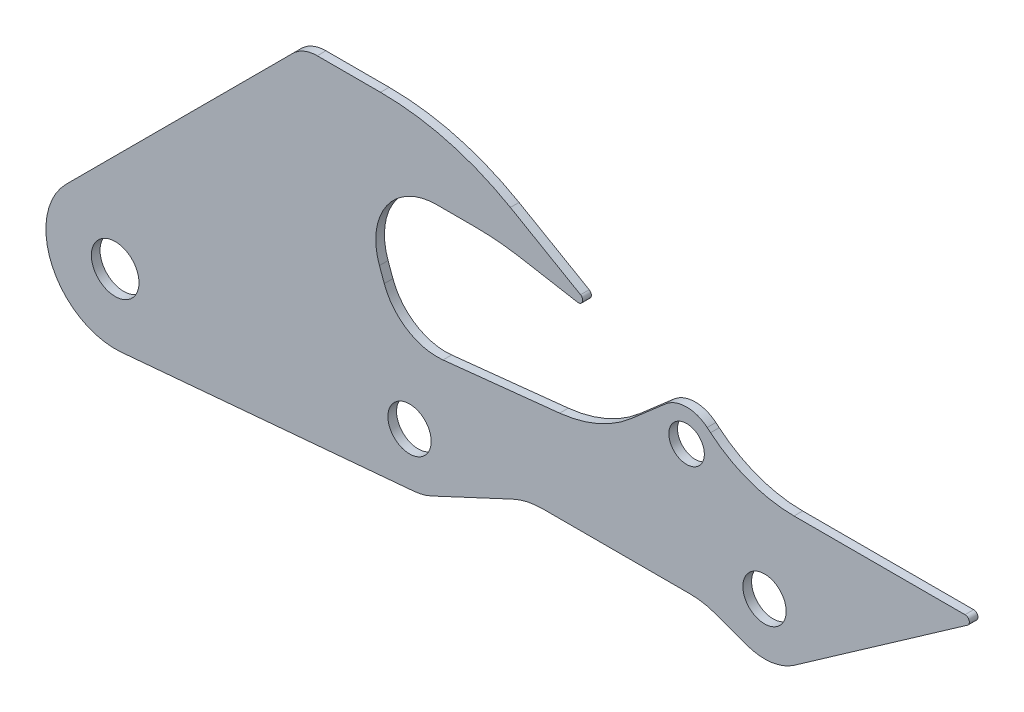
SolidWorks part; units mm, degrees
ref_plane "Plane1" through (0, 0, 0) normal (0, 0, 1) x (1, 0, 0)
ref_plane "Plane2" through (0, 0, 0) normal (0, 1, 0) x (1, 0, 0)
ref_plane "Plane3" through (0, 0, 0) normal (1, 0, 0) x (0, 0, -1)
sketch "Sketch1" plane through (0, 0, 0) normal (0, 0, 1) x (1, 0, 0)
  line L0 (170.8498, -23.8937) -> (168.6162, 52.0491) construction
  line L1 (7.0497, -79.6888) -> (345.2873, -49.7666)
  line L2 (729.4788, -11.3816) -> (692.5627, 2.0548)
  line L3 (493.7175, 7) -> (664.5171, 7)
  line L4 (0, 0) -> (750, 45) construction
  line L5 (0, 0) -> (283.2713, 0) construction
  line L6 (784.4146, -4.1491) -> (984.4315, 135.9042)
  line L7 (365.3571, -44.3785) -> (459.0628, -0.6828)
  line L8 (310.7829, 140.7687) -> (305.2178, 156.0586)
  line L9 (687.6567, 180.0933) -> (683.7831, 183.3436)
  line L11 (537.5, 243.0296) -> (456.4782, 289.8076)
  line L12 (-56.5685, 56.5685) -> (205.1472, 318.2843)
  line L13 (306.4782, 330) -> (233.4315, 330)
  line L14 (635.7258, 182.9243) -> (596.1115, 148.4881)
  line L15 (513.3819, 112.5162) -> (378.6573, 98.3561)
  line L16 (534.1318, 233.7755) -> (467.9657, 245.4423)
  line L17 (415.8713, 250) -> (370.9963, 250)
  line L18 (750, 45) -> (833, 45) construction
  line L19 (784.0749, 145) -> (981.5636, 145)
  circle A0 centre (0, 0) radius 27.5
  circle A1 centre (340, 10) radius 25
  arc A2 (-56.5685, 56.5685) -> (7.0497, -79.6888) centre (0, 0) ccw
  arc A3 (981.5636, 145) -> (984.4315, 135.9042) centre (981.5636, 140) cw
  circle A4 centre (750, 45) radius 25
  arc A5 (784.4146, -4.1491) -> (729.4788, -11.3816) centre (750, 45) cw
  arc A6 (378.6573, 98.3561) -> (310.7829, 140.7687) centre (371.8629, 163) cw
  arc A7 (345.2873, -49.7666) -> (365.3571, -44.3785) centre (340, 10) ccw
  arc A8 (205.1472, 318.2843) -> (233.4315, 330) centre (233.4315, 290) cw
  arc A9 (456.4782, 289.8076) -> (306.4782, 330) centre (306.4782, 30) ccw
  arc A10 (534.1318, 233.7755) -> (537.5, 243.0296) centre (535, 238.6995) ccw
  arc A11 (683.7831, 183.3436) -> (635.7258, 182.9243) centre (660, 155) ccw
  circle A12 centre (660, 155) radius 20.5
  arc A13 (493.7175, 7) -> (459.0628, -0.6828) centre (493.7175, -75) ccw
  arc A14 (664.5171, 7) -> (692.5627, 2.0548) centre (664.5171, -75) cw
  arc A15 (784.0749, 145) -> (687.6567, 180.0933) centre (784.0749, 295) cw
  arc A16 (596.1115, 148.4881) -> (513.3819, 112.5162) centre (497.7026, 261.6945) cw
  arc A17 (370.9963, 250) -> (305.2178, 156.0586) centre (370.9963, 180) ccw
  arc A18 (467.9657, 245.4423) -> (415.8713, 250) centre (415.8713, -50) ccw
  point P36 (216.8629, 330)
  point P39 (386.8629, 330)
  dimension "D1" = 340
  dimension "D2" = 55
  dimension "D3" = 80
  dimension "D4" = 60
  dimension "D7" = 50
  dimension "D8" = 750
  dimension "D16" = 60
  dimension "D23" = 70
  dimension "D24" = 40
  dimension "D25" = 90
  dimension "D26" = 163
  dimension "D28" = 20
  dimension "D29" = 41
  dimension "D30" = 82
  dimension "D33" = 35
  dimension "D34" = 150
  dimension "D18" = 100
  dimension "D27" = 50
  dimension "D19" = 25
  dimension "D36" = 82
  dimension "D37" = 5
  dimension "D38" = 150
  dimension "D20" = 65
  dimension "D6" = 5
  dimension "D31" = 37
  dimension "D40" = 540
  dimension "D42" = 300
  dimension "D43" = 300
  dimension "D5" = 38
  dimension "D9" = 45
  dimension "D10" = 45
  dimension "D11" = 330
  dimension "D12" = 30
  dimension "D13" = 110
  dimension "D14" = 170
  dimension "D15" = 6
  dimension "D17" = 35
  dimension "D21" = 155
  dimension "D22" = 80
  dimension "D32" = 40
  dimension "D35" = 10
  dimension "D39" = 70
  dimension "D41" = 20
extrude "Base-Extrude" add sketch "Sketch1" against normal blind 10
